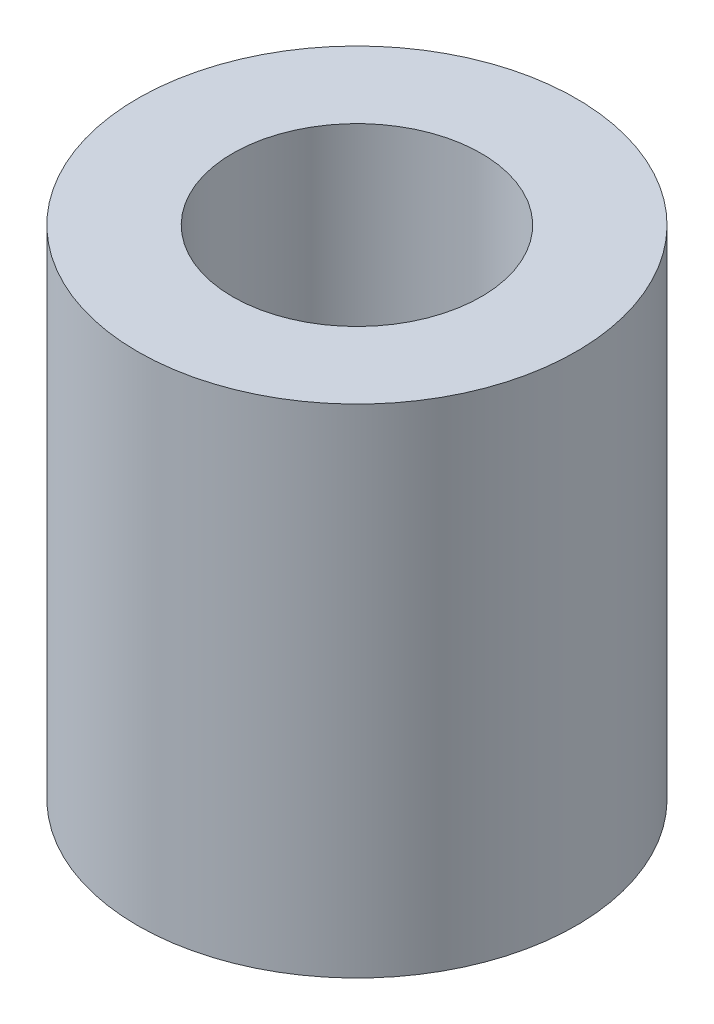
SolidWorks part; units mm, degrees
ref_plane "Front Plane" through (0, 0, 0) normal (0, 0, 1) x (1, 0, 0)
ref_plane "Top Plane" through (0, 0, 0) normal (0, 1, 0) x (1, 0, 0)
ref_plane "Right Plane" through (0, 0, 0) normal (1, 0, 0) x (0, 0, -1)
sketch "Sketch1" plane through (0, 0, 0) normal (0, 1, 0) x (1, 0, 0)
  circle A0 centre (0, 0) radius 4.25
  circle A1 centre (0, 0) radius 7.5
  dimension "D1" = 8.5
  dimension "D2" = 15
extrude "Boss-Extrude1" add sketch "Sketch1" along normal blind 17
